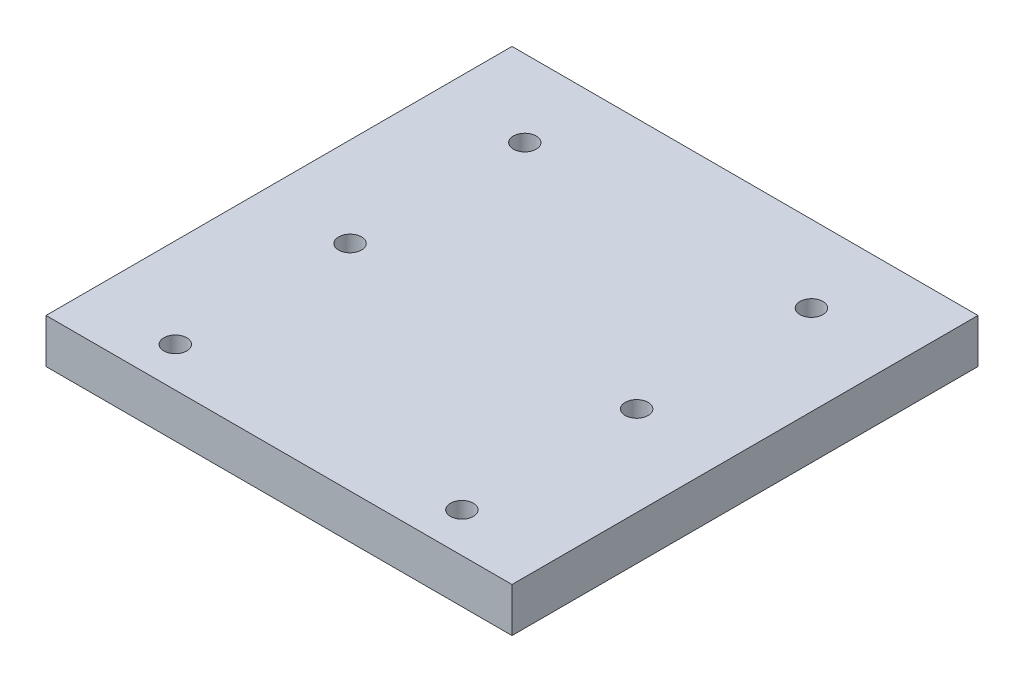
SolidWorks part; units mm, degrees
ref_plane "Front Plane" through (0, 0, 0) normal (0, 0, 1) x (1, 0, 0)
ref_plane "Top Plane" through (0, 0, 0) normal (0, 1, 0) x (1, 0, 0)
ref_plane "Right Plane" through (0, 0, 0) normal (1, 0, 0) x (0, 0, -1)
sketch "Sketch1" plane through (0, 0, 0) normal (0, 1, 0) x (1, 0, 0)
  line L1 (-25.4, 25.4) -> (25.4, 25.4)
  line L2 (-25.4, 25.4) -> (-25.4, -25.4)
  line L3 (-25.4, -25.4) -> (25.4, -25.4)
  line L4 (25.4, 25.4) -> (25.4, -25.4)
  line L5 (-25.4, 25.4) -> (25.4, -25.4) construction
  line L6 (-25.4, -25.4) -> (25.4, 25.4) construction
  point P0 (0, 0)
  dimension "D1" = 50.8
  dimension "D2" = 50.8
extrude "Boss-Extrude1" add sketch "Sketch1" against normal blind 4.826
sketch "Sketch2" plane through (0, 0, 0) normal (0, 1, 0) x (1, 0, 0)
  line L0 (25.4, 25.4) -> (-25.4, 25.4) construction
  circle A0 centre (-15.621, 17.018) radius 1.25
  circle A1 centre (15.621, 17.018) radius 1.25
  dimension "D3" = 2.5
  dimension "D1" = 31.242
  dimension "D2" = 15.621
  dimension "D4" = 8.382
extrude "Cut-Extrude1" cut sketch "Sketch2" against normal blind 9.906
pattern_linear "LPattern1" count 3 spacing 19.05 along (0, 0, 1) of "Cut-Extrude1"
